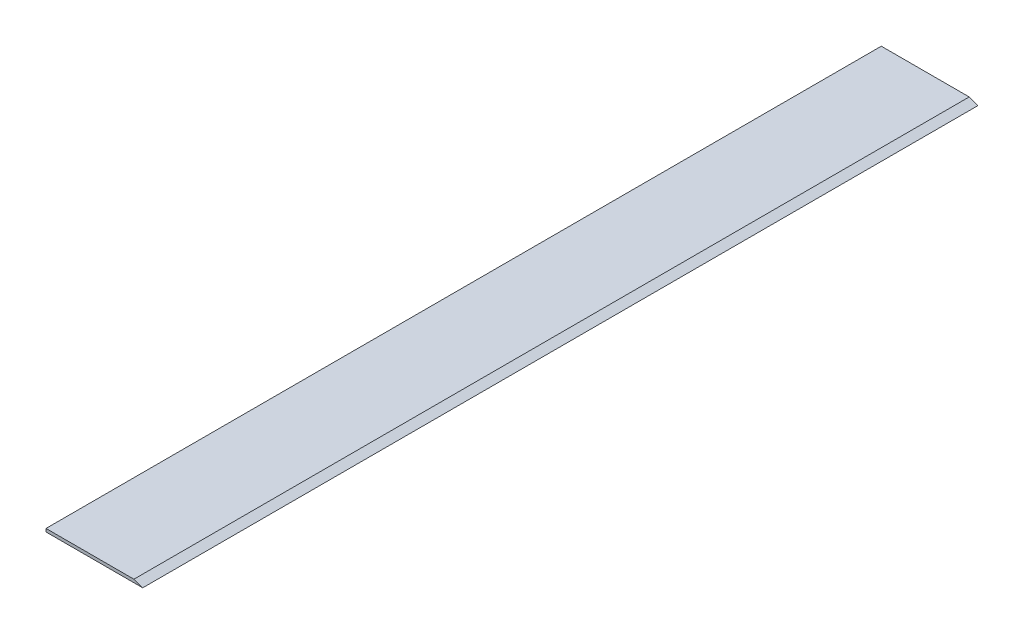
SolidWorks part; units mm, degrees
ref_plane "Alzado" through (0, 0, 0) normal (0, 0, 1) x (1, 0, 0)
ref_plane "Planta" through (0, 0, 0) normal (0, 1, 0) x (1, 0, 0)
ref_plane "Vista lateral" through (0, 0, 0) normal (1, 0, 0) x (0, 0, -1)
sketch "Croquis1" plane through (0, 0, 0) normal (0, 0, 1) x (1, 0, 0)
  line L0 (0, 0) -> (22, 0)
  line L1 (22, 0) -> (20, 0.7)
  line L2 (20, 0.7) -> (0, 0.7)
  line L3 (0, 0.7) -> (0, 0)
  dimension "D1" = 0.7
  dimension "D2" = 22
  dimension "D3" = 2
  dimension "D4" = 19.29
extrude "Saliente-Extruir1" add sketch "Croquis1" along normal blind 190
